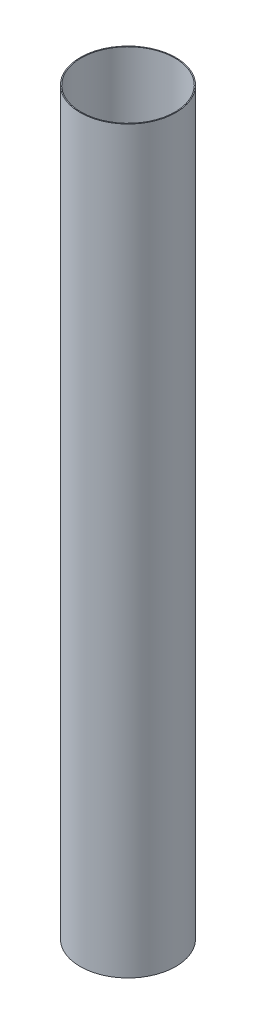
SolidWorks part; units mm, degrees
material "Thornel Mat VMA"
ref_plane "Front Plane" through (0, 0, 0) normal (0, 0, 1) x (1, 0, 0)
ref_plane "Top Plane" through (0, 0, 0) normal (0, 1, 0) x (1, 0, 0)
ref_plane "Right Plane" through (0, 0, 0) normal (1, 0, 0) x (0, 0, -1)
sketch "Sketch1" plane through (0, 0, 0) normal (0, 1, 0) x (1, 0, 0)
  circle A0 centre (0, 0) radius 66.04
  circle A1 centre (0, 0) radius 67.31
  dimension "D1" = 1.27
  dimension "D2" = 132.08
extrude "Boss-Extrude1" add sketch "Sketch1" along normal blind 1041.4
